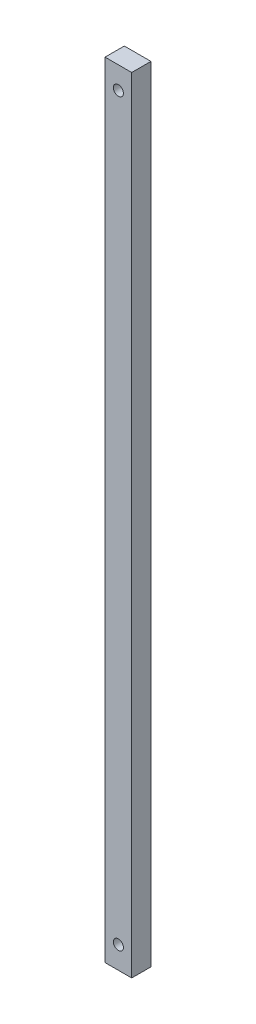
SolidWorks part; units mm, degrees
ref_plane "前视基准面" through (0, 0, 0) normal (0, 0, 1) x (1, 0, 0)
ref_plane "上视基准面" through (0, 0, 0) normal (0, 1, 0) x (1, 0, 0)
ref_plane "右视基准面" through (0, 0, 0) normal (1, 0, 0) x (0, 0, -1)
sketch "草图1" plane through (0, 0, 0) normal (0, 0, 1) x (1, 0, 0)
  line L1 (0, 0) -> (9, 0)
  line L2 (0, 0) -> (0, 265)
  line L3 (0, 265) -> (9, 265)
  line L4 (9, 0) -> (9, 265)
  dimension "D1" = 9
  dimension "D2" = 265
extrude "凸台-拉伸1" add sketch "草图1" along normal blind 6.5
hole_wizard "M3 六角凹头螺钉的柱形沉头孔1" positions "草图2" profile "草图3" counterbore size "M3" standard "ISO"
sketch "草图2" plane through (0, 0, 0) normal (0, 0, -1) x (-1, 0, 0)
  line L0 (0, 265) -> (0, 0) construction
  line L1 (0, 0) -> (-9, 0) construction
  line L2 (-9, 265) -> (0, 265) construction
  point P0 (-4.5, 7.5)
  point P2 (-4.5, 257.5)
  dimension "D1" = 4.5
  dimension "D2" = 7.5
  dimension "D3" = 7.5
sketch "草图3" plane through (4.5, 7.5, 0) normal (1, 0, 0) x (0, 1, 0)
  line L0 (0, 0) -> (0, 11.1215)
  line L1 (0, 11.1215) -> (1.7, 10.1)
  line L2 (1.7, 10.1) -> (1.7, 3.4)
  line L3 (1.7, 3.4) -> (3.25, 3.4)
  line L4 (3.25, 3.4) -> (3.25, 0)
  line L5 (3.25, 0) -> (0, 0)
  line L10 (0, 11.1215) -> (-1.7, 10.1) construction
  line L11 (0, -6.35) -> (0, 107.95) construction
  dimension "孔直径" = 3.4
  dimension "孔深度" = 10.1
  dimension "柱形沉头孔直径" = 6.5
  dimension "柱形沉头孔深度" = 3.4
  dimension "导头角度" = 118
